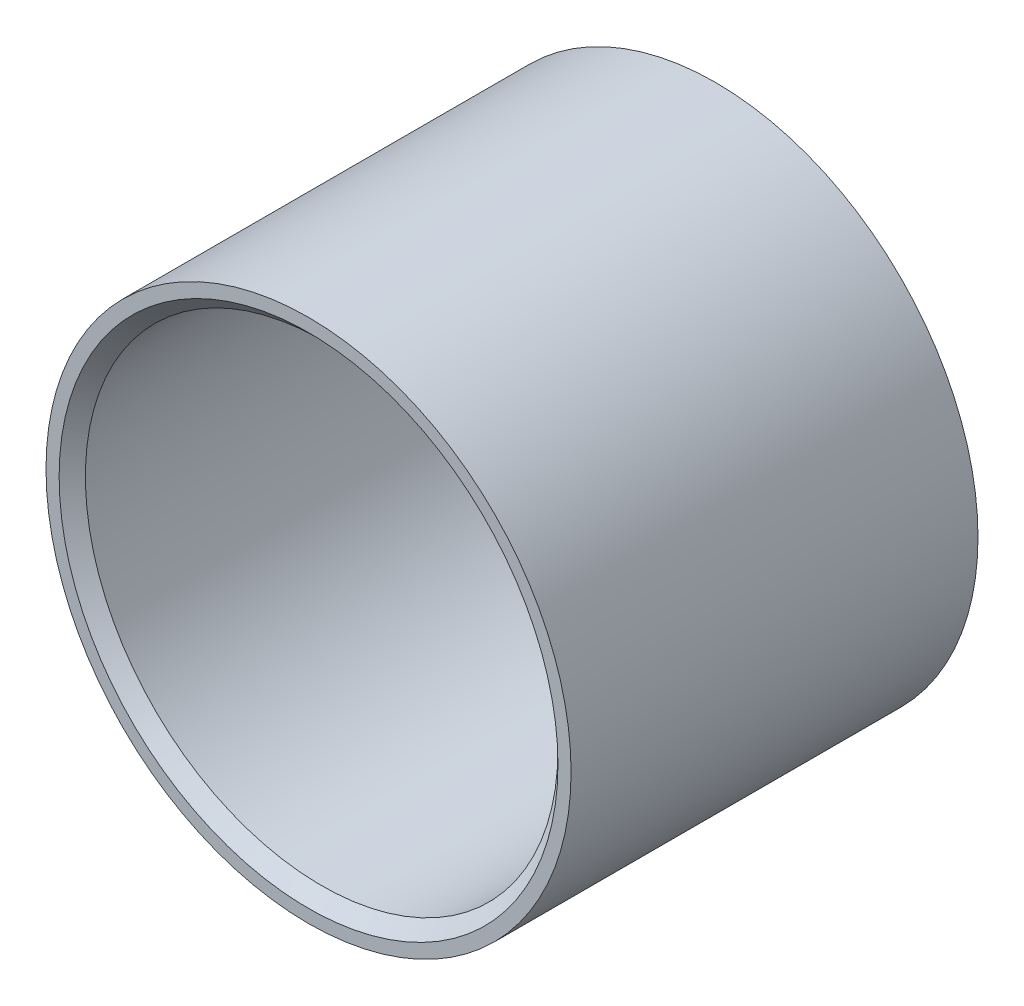
SolidWorks part; units mm, degrees
ref_plane "Front Plane" through (0, 0, 0) normal (0, 0, 1) x (1, 0, 0)
ref_plane "Top Plane" through (0, 0, 0) normal (0, 1, 0) x (1, 0, 0)
ref_plane "Right Plane" through (0, 0, 0) normal (1, 0, 0) x (0, 0, -1)
sketch "Sketch1" plane through (0, 0, 0) normal (0, 0, 1) x (1, 0, 0)
  circle A0 centre (0, 0) radius 9
  circle A2 centre (0, 0) radius 10
  dimension "D1" = 18
  dimension "D2" = 1
extrude "Boss-Extrude1" add sketch "Sketch1" along normal blind 15.5
chamfer "Chamfer1" distance 0.5 angle 45 2 edges at (9, 0, 0) (9, 0, 15.5)
